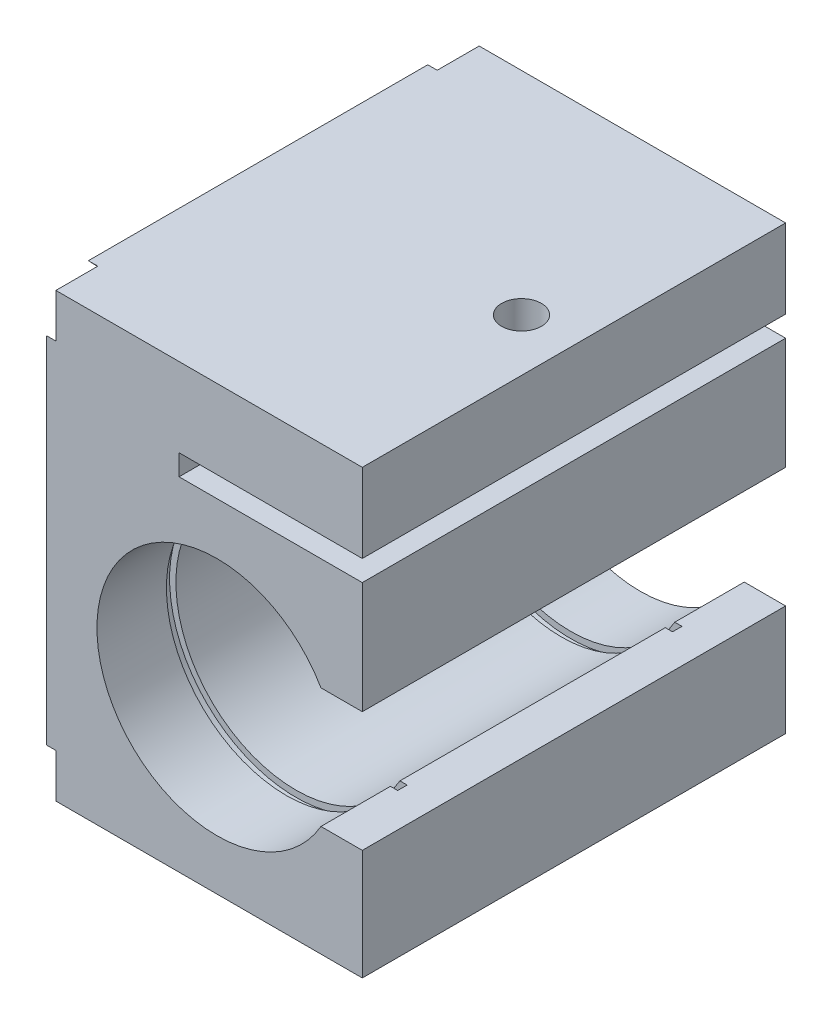
SolidWorks part; units mm, degrees
material "AISI 1020"
ref_plane "Front Plane" through (0, 0, 0) normal (0, 0, 1) x (1, 0, 0)
ref_plane "Top Plane" through (0, 0, 0) normal (0, 1, 0) x (1, 0, 0)
ref_plane "Right Plane" through (0, 0, 0) normal (1, 0, 0) x (0, 0, -1)
sketch "Sketch11" plane through (0, 0, 0) normal (0, 0, 1) x (1, 0, 0)
  line L1 (-25, -35) -> (25, -35)
  line L2 (-25, -35) -> (-25, 35)
  line L3 (-25, 35) -> (25, 35)
  line L4 (25, -35) -> (25, 35)
  line L5 (-25, -35) -> (25, 35) construction
  line L6 (-25, 35) -> (25, -35) construction
  point P0 (0, 0)
  dimension "D1" = 50
  dimension "D2" = 70
extrude "Boss-Extrude4" add sketch "Sketch11" along normal blind 67
sketch "Sketch12" plane through (0, 0, 67) normal (0, 0, 1) x (1, 0, 0)
  line L0 (25, -35) -> (25, 35) construction
  line L1 (-25, 35) -> (-25, -35) construction
  line L2 (-25, -35) -> (25, -35) construction
  line L5 (25, 22.5) -> (-4, 22.5)
  line L6 (25, 22.5) -> (25, 19.2)
  line L7 (25, 19.2) -> (-4, 19.2)
  line L8 (-4, 22.5) -> (-4, 19.2)
  line L9 (25, 35) -> (-25, 35) construction
  line L10 (2, -8) -> (25, -8) construction
  line L11 (18.4545, -17.5) -> (25, -17.5)
  line L12 (25, -35) -> (25, 35)
  line L13 (25, 35) -> (-25, 35)
  line L14 (-25, 35) -> (-25, -35)
  line L15 (-25, -35) -> (25, -35)
  line L16 (25, -17.5) -> (25, 1.5)
  line L20 (18.4545, 1.5) -> (25, 1.5)
  line L21 (2, 1.5) -> (42.2175, 1.5) construction
  line L22 (2, -8) -> (42.2175, -8) construction
  line L23 (2, -17.5) -> (42.2175, -17.5) construction
  arc A0 (18.4545, 1.5) -> (18.4545, -17.5) centre (2, -8) ccw
  dimension "D1" = 38
  dimension "D2" = 27
  dimension "D3" = 27
  dimension "D4" = 12.5
  dimension "D5" = 3.3
  dimension "D7" = 29
  dimension "D6" = 0
  dimension "D8" = 9.5
  dimension "D9" = 9.5
extrude "Cut-Extrude7" cut sketch "Sketch12" against normal through all
sketch "Sketch13" plane through (-25, 0, 0) normal (-1, 0, 0) x (0, 0, 1)
  line L0 (0, -35) -> (67, 35) construction
  line L1 (0, 35) -> (67, -35) construction
  line L2 (0, 28.0581) -> (26.8556, 0)
  line L3 (6.6444, -35) -> (33.5, -6.9419)
  line L4 (6.6444, 35) -> (33.5, 6.9419)
  line L5 (0, -28.0581) -> (26.8556, 0)
  line L6 (-3.4676, 31.681) -> (63.5324, -38.319) construction
  line L7 (3.4676, 38.319) -> (70.4676, -31.681) construction
  line L8 (-3.4676, -31.681) -> (63.5324, 38.319) construction
  line L9 (3.4676, -38.319) -> (70.4676, 31.681) construction
  line L10 (0, 35) -> (0, -35)
  line L11 (0, -35) -> (67, -35)
  line L12 (67, -35) -> (67, 35)
  line L13 (67, 35) -> (0, 35)
  line L14 (0, 35) -> (0, -35)
  line L15 (0, -35) -> (67, -35)
  line L16 (67, -35) -> (67, 35)
  line L17 (67, 35) -> (0, 35)
  line L18 (33.5, -6.9419) -> (60.3556, -35)
  line L19 (33.5, 6.9419) -> (60.3556, 35)
  line L20 (40.1444, 0) -> (67, -28.0581)
  line L21 (40.1444, 0) -> (67, 28.0581)
  line M8 (0, 35) -> (0, -35)
  line M9 (0, -35) -> (67, -35)
  line M10 (67, -35) -> (67, 35)
  line M11 (67, 35) -> (0, 35)
  dimension "D1" = 4.8
  dimension "D2" = 4.8
  dimension "D3" = 0
extrude "Cut-Extrude8" cut sketch "Sketch13" against normal blind 1.5 contours L20 L21 L19 L4 L2 L5 L3 L18 L15 M10 M11 M8 M9
sketch "Sketch14" plane through (0, 35, 0) normal (0, 1, 0) x (1, 0, 0)
  line L0 (25, -67) -> (25, 0) construction
  line L1 (25, 0) -> (-23.5, 0) construction
  circle A0 centre (16.7, -33.5) radius 3.15
  dimension "D1" = 6.3
  dimension "D3" = 33.5
  dimension "D2" = 8.3
extrude "Cut-Extrude9" cut sketch "Sketch14" against normal up to surface (12.5 mm away) up to face at (10.5, 22.5, 33.5)
sketch3d "3DSketch1"
  point P0 (21.1232, -30.213, 67)
ref_plane "Plane8" through (0, 0, 54.5) normal (0, 0, 1) x (1, 0, 0)
sketch "Sketch15" plane through (0, 0, 54.5) normal (0, 0, 1) x (1, 0, 0)
  circle A0 centre (2, -8) radius 20
extrude "Cut-Extrude11" cut sketch "Sketch15" along normal blind 1.5
ref_plane "Plane10" through (0, 0, 33.5) normal (0, 0, 1) x (1, 0, 0)
mirror "Mirror4" about plane through (0, 0, 33.5) normal (0, 0, 1) of "Cut-Extrude11"
equation "\"A\"= 50"
equation "\"B\" = 70"
equation "\"D1@Sketch11\"=\"A\""
equation "\"D2@Sketch11\"=\"B\""
